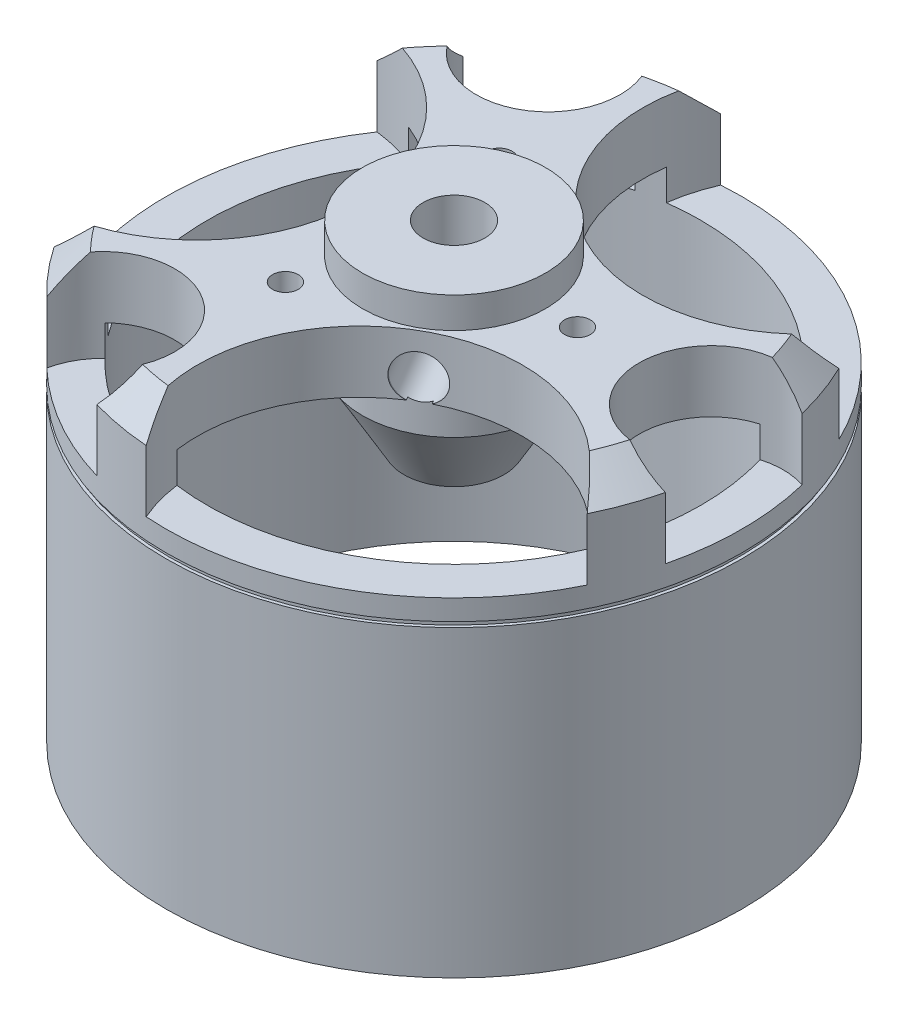
SolidWorks part; units mm, degrees
ref_plane "Front Plane" through (0, 0, 0) normal (0, 0, 1) x (1, 0, 0)
ref_plane "Top Plane" through (0, 0, 0) normal (0, 1, 0) x (1, 0, 0)
ref_plane "Right Plane" through (0, 0, 0) normal (1, 0, 0) x (0, 0, -1)
sketch "Sketch1" plane through (0, 0, 0) normal (0, 1, 0) x (1, 0, 0)
  circle A0 centre (0, 0) radius 14
  dimension "D1" = 28
extrude "Boss-Extrude1" add sketch "Sketch1" along normal blind 20.5
sketch "Sketch2" plane through (0, 0, 0) normal (0, -1, 0) x (1, 0, 0)
  circle A0 centre (0, 0) radius 12
  circle A1 centre (0, 0) radius 14 construction
  dimension "D1" = 2
extrude "Cut-Extrude1" cut sketch "Sketch2" against normal offset from surface (17.5 mm away) 3 up to face at (0, 20.5, 14)
chamfer "Chamfer1" distance 1.5 angle 45 1 edges at (0, 20.5, 14)
sketch "Sketch3" plane through (0, 0, 0) normal (1, 0, 0) x (0, 0, -1)
  line L0 (12.5, 20.5) -> (-12.5, 20.5) construction
  line L1 (13.85, 15) -> (14, 15)
  line L2 (13.85, 15) -> (13.85, 14.75)
  line L3 (13.85, 14.75) -> (14, 14.75)
  line L4 (14, 15) -> (14, 14.75)
  line L5 (14, 0) -> (14, 19) construction
  line L6 (0, 20.5) -> (0, 0) construction
  dimension "D1" = 5.5
  dimension "D2" = 0.25
  dimension "D3" = 0.15
revolve "Cut-Revolve1" cut sketch "Sketch3" angle 360 about L6
sketch "Sketch4" plane through (0, 20.5, 0) normal (0, 1, 0) x (1, 0, 0)
  circle A0 centre (0, 0) radius 4.45
  dimension "D1" = 8.9
extrude "Boss-Extrude2" add sketch "Sketch4" along normal blind 1.5 and the other way offset from surface (4.5 mm away) 1.5 other way up to face at (0, 17.5, 12)
sketch "Sketch10" plane through (0, 16, 0) normal (0, -1, 0) x (1, 0, 0)
  circle A1 centre (0, 0) radius 4.45
  circle A2 centre (0, 0) radius 4.45
  dimension "D1" = 0
extrude "Boss-Extrude3" add sketch "Sketch10" along normal blind 3.5 draft 30
sketch "Sketch5" plane through (0, 22, 0) normal (0, 1, 0) x (1, 0, 0)
  circle A0 centre (0, 0) radius 1.5
  dimension "D1" = 3
extrude "Cut-Extrude2" cut sketch "Sketch5" against normal through all
sketch "Sketch6" plane through (0, 20.5, 0) normal (0, 1, 0) x (1, 0, 0)
  line L0 (0, 0) -> (-14, 0) construction
  line L1 (0, 0) -> (-7, 12.1244) construction
  line L2 (0, 0) -> (7, 12.1244) construction
  line L3 (0, 0) -> (14, 0) construction
  line L4 (0, 0) -> (7, -12.1244) construction
  line L5 (0, 0) -> (-7, -12.1244) construction
  circle A0 centre (0, 0) radius 14 construction
  circle A1 centre (0, 0) radius 14
  arc A2 (-11.5936, -7.8478) -> (-11.5936, 7.8478) centre (-12.5, 0) ccw
  circle A3 centre (0, 0) radius 12.5 construction
  arc A4 (12.5932, -6.1164) -> (-0.9996, -13.9643) centre (6.25, -10.8253) ccw
  arc A5 (-0.9996, 13.9643) -> (12.5932, 6.1164) centre (6.25, 10.8253) ccw
  arc A6 (-3.9225, -13.4393) -> (-9.6775, -10.1166) centre (-6.25, -10.8253) ccw
  arc A7 (-9.6775, 10.1166) -> (-3.9225, 13.4393) centre (-6.25, 10.8253) ccw
  arc A8 (13.6, 3.3226) -> (13.6, -3.3226) centre (12.5, 0) ccw
  point P12 (0, 0)
  point P23 (0, 0)
  circle M1 centre (0, 0) radius 12.5
  dimension "D2" = 15.8
  dimension "D3" = 7
  dimension "D1" = 6
extrude "Cut-Extrude3" cut sketch "Sketch6" against normal blind 4.5 contours A2 M1 | A1 A2 M1 | A6 M1 | A1 A6 M1 | A1 A4 M1 | A4 M1 | A8 M1 | A1 A8 M1 | A5 A1 M1 | A5 M1 | A7 M1 | A7 A1 M1
hole_wizard "M1.6x0.35 Tapped Hole1" positions "3DSketch1" profile "Sketch7" tap size "M1.6x0.35" standard "ANSI Metric"
sketch3d "3DSketch1"
  line L0 (0, 20.5, 0) -> (14, 20.5, 0) construction
  line L1 (0, 20.5, 0) -> (-7, 20.5, 12.1244) construction
  line L2 (0, 20.5, 0) -> (-7, 20.5, -12.1244) construction
  point P0 (6, 20.5, 0)
  point P4 (-3, 20.5, 5.1962)
  point P8 (-3, 20.5, -5.1962)
  dimension "D1" = 6
  dimension "D2" = 6
  dimension "D3" = 6
sketch "Sketch7" plane through (6, 20.5, 0) normal (1, 0, 0) x (0, 0, 1)
  line L0 (0, 0) -> (0, 4.6255)
  line L1 (0, 4.6255) -> (0.625, 4.25)
  line L2 (0.625, 4.25) -> (0.625, 0)
  line L5 (0.625, 0) -> (0, 0)
  line L10 (0, 4.6255) -> (-0.625, 4.25) construction
  line L11 (0, -6.35) -> (0, 107.95) construction
  dimension "Tap Drill Dia." = 1.25
  dimension "Tap Drill Depth" = 4.25
  dimension "Drill Angle" = 118
ref_plane "Plane3" through (0, 18.5, 0) normal (0, 1, 0) x (1, 0, 0)
sketch "Sketch16" plane through (0, 18.5, 0) normal (0, 1, 0) x (1, 0, 0)
  line L0 (0, 0) -> (6.25, -10.8253) construction
  point P0 (0, 0)
hole_wizard "M2 Clearance Hole4" positions "3DSketch2" profile "Sketch14" hole size "M2" standard "ISO"
sketch3d "3DSketch2"
  line L0 (0, 18.5, 0) -> (6.25, 18.5, 10.8253) construction
  point P0 (-4.6, 18.5, 0)
  point P2 (2.3, 18.5, 3.9837)
  point P5 (-4.6, 18.5, 0)
sketch "Sketch14" plane through (-4.6, 18.5, 0) normal (0, 1, 0) x (0, 0, 1)
  line L0 (0, 0) -> (0, 4.1609)
  line L1 (0, 4.1609) -> (1.1, 3.5)
  line L2 (1.1, 3.5) -> (1.1, 0)
  line L5 (1.1, 0) -> (0, 0)
  line L10 (0, 4.1609) -> (-1.1, 3.5) construction
  line L11 (0, -6.35) -> (0, 107.95) construction
  dimension "Hole Dia." = 2.2
  dimension "Hole Depth" = 3.5
  dimension "Drill Angle" = 118
